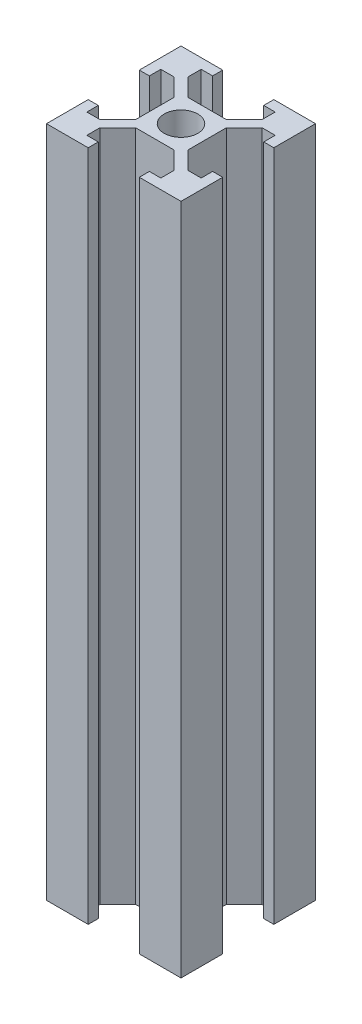
SolidWorks part; units mm, degrees
ref_plane "前视基准面" through (0, 0, 0) normal (0, 0, 1) x (1, 0, 0)
ref_plane "上视基准面" through (0, 0, 0) normal (0, 1, 0) x (1, 0, 0)
ref_plane "右视基准面" through (0, 0, 0) normal (1, 0, 0) x (0, 0, -1)
sketch "草图1" plane through (0, 0, 0) normal (0, 1, 0) x (1, 0, 0)
  line L0 (-6.5607, 5.5) -> (-3.9, 2.8393)
  line L1 (-10, 10) -> (10, 10)
  line L2 (-10, 10) -> (-10, -10)
  line L3 (-10, -10) -> (10, -10)
  line L4 (10, 10) -> (10, -10)
  line L5 (-10, 10) -> (10, -10) construction
  line L6 (-10, -10) -> (10, 10) construction
  line L7 (-3.9, 3.9) -> (3.9, 3.9)
  line L8 (-3.9, 3.9) -> (-3.9, -3.9)
  line L9 (-3.9, -3.9) -> (3.9, -3.9)
  line L10 (3.9, 3.9) -> (3.9, -3.9)
  line L11 (-3.9, 3.9) -> (3.9, -3.9) construction
  line L12 (-3.9, -3.9) -> (3.9, 3.9) construction
  line L13 (-10, 10) -> (-5.5, 10)
  line L14 (-10, 10) -> (-10, 5.5)
  line L15 (-10, 5.5) -> (-5.5, 5.5)
  line L16 (-5.5, 10) -> (-5.5, 5.5)
  line L17 (-10, 5.5) -> (-8.5, 5.5)
  line L18 (-10, 5.5) -> (-10, 3.8)
  line L19 (-10, 3.8) -> (-8.5, 3.8)
  line L20 (-8.5, 5.5) -> (-8.5, 3.8)
  line L21 (-5.5, 6.5607) -> (-2.8393, 3.9)
  line L22 (-3.8, 10) -> (-3.8, 8.5)
  line L23 (-5.5, 8.5) -> (-3.8, 8.5)
  line L24 (0, 10) -> (0, -10) construction
  line L25 (5.5, 8.5) -> (3.8, 8.5)
  line L26 (3.8, 10) -> (3.8, 8.5)
  line L27 (5.5, 6.5607) -> (2.8393, 3.9)
  line L28 (6.5607, 5.5) -> (3.9, 2.8393)
  line L29 (10, 3.8) -> (8.5, 3.8)
  line L30 (8.5, 5.5) -> (8.5, 3.8)
  line L31 (10, 5.5) -> (8.5, 5.5)
  line L32 (10, 5.5) -> (10, 3.8)
  line L33 (10, 5.5) -> (5.5, 5.5)
  line L34 (5.5, 10) -> (5.5, 5.5)
  line L35 (10, 10) -> (5.5, 10)
  line L36 (10, 10) -> (10, 5.5)
  line L37 (-10, 0) -> (10, 0) construction
  line L38 (-10, -3.8) -> (-8.5, -3.8)
  line L39 (-8.5, -5.5) -> (-8.5, -3.8)
  line L40 (-10, -5.5) -> (-5.5, -5.5)
  line L41 (-6.5607, -5.5) -> (-3.9, -2.8393)
  line L42 (-5.5, -6.5607) -> (-2.8393, -3.9)
  line L43 (-5.5, -10) -> (-5.5, -5.5)
  line L44 (-5.5, -8.5) -> (-3.8, -8.5)
  line L45 (-3.8, -10) -> (-3.8, -8.5)
  line L46 (3.8, -10) -> (3.8, -8.5)
  line L47 (6.5607, -5.5) -> (3.9, -2.8393)
  line L48 (5.5, -6.5607) -> (2.8393, -3.9)
  line L49 (-10, 10) -> (10, 10)
  line L50 (-10, -10) -> (10, -10)
  line L51 (5.5, -8.5) -> (3.8, -8.5)
  line L52 (5.5, -10) -> (5.5, -5.5)
  line L53 (10, -5.5) -> (5.5, -5.5)
  line L54 (10, -3.8) -> (8.5, -3.8)
  line L55 (8.5, -5.5) -> (8.5, -3.8)
  circle A0 centre (0, 0) radius 2.5
  dimension "D1" = 5
  dimension "D2" = 20
  dimension "D3" = 20
  dimension "D4" = 7.8
  dimension "D5" = 4.5
  dimension "D6" = 1.7
  dimension "D7" = 0.75
  dimension "D8" = 1.5
extrude "凸台-拉伸1" add sketch "草图1" along normal blind 100 contours L1 L34 L33 L31 L4 | L4 L31 L30 L29 | L34 L27 L7 L10 L28 L33 | L34 L1 L26 L25 | L10 L7 L8 L9 A0 | L16 L23 L22 L1 | L16 L1 L2 L15 | L20 L15 L2 L19 | L21 L16 L15 L0 L8 L7 | L3 L43 L40 L2 | L3 L45 L44 L43 | L2 L40 L39 L38 | L43 L42 L9 L8 L41 L40 | L53 L47 L10 L9 L48 L52 | L4 L53 L52 L50 | L55 L53 L4 L54 | L3 L52 L51 L46
